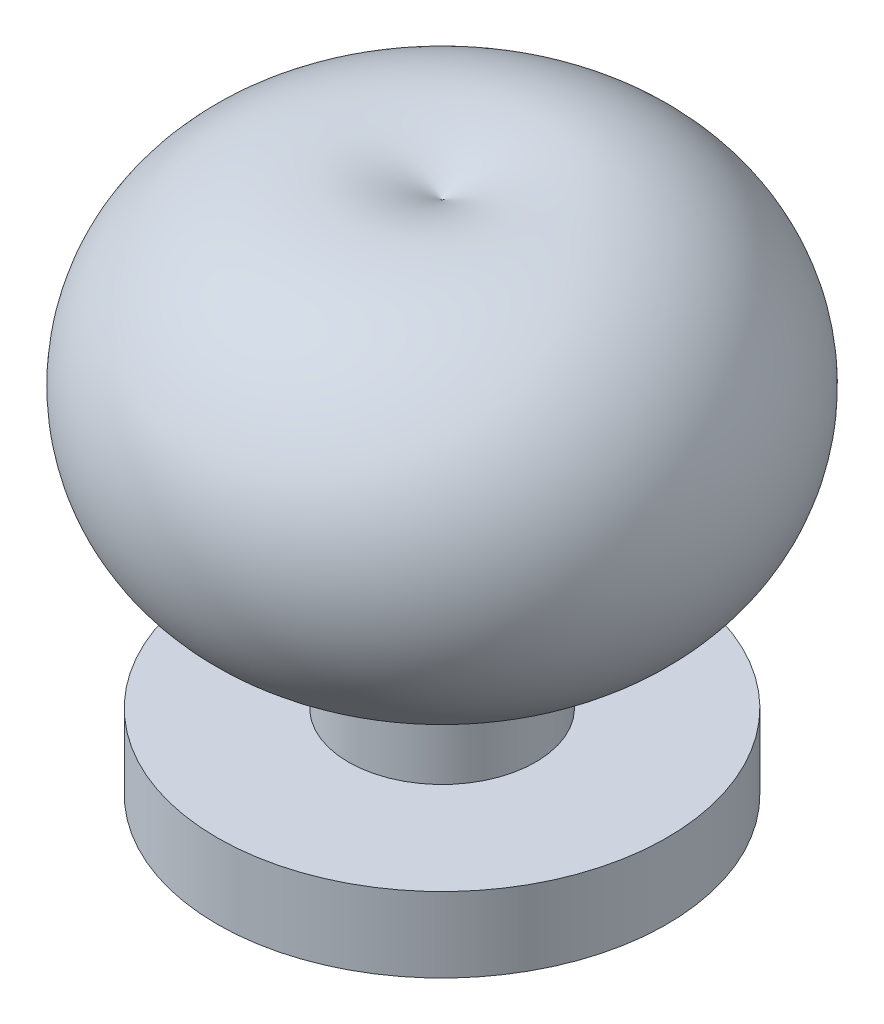
SolidWorks part; units mm, degrees
ref_plane "Front Plane" through (0, 0, 0) normal (0, 0, 1) x (1, 0, 0)
ref_plane "Top Plane" through (0, 0, 0) normal (0, 1, 0) x (1, 0, 0)
ref_plane "Right Plane" through (0, 0, 0) normal (1, 0, 0) x (0, 0, -1)
sketch "Sketch1" plane through (0, 0, 0) normal (1, 0, 0) x (0, 0, -1)
  line L0 (0, 0) -> (6, 0)
  line L1 (6, 0) -> (6, 2)
  line L2 (6, 2) -> (2.5, 2)
  line L3 (2.5, 2) -> (2.5, 4.5)
  line L4 (0, 13.75) -> (0, 0)
  arc A0 (2.5, 4.5) -> (0, 13.75) centre (2.5, 9.4628) ccw
  dimension "D1" = 6
  dimension "D2" = 2
  dimension "D3" = 2.5
  dimension "D4" = 2.5
  dimension "D5" = 13.75
revolve "Revolve1" add sketch "Sketch1" angle 360 about L4
